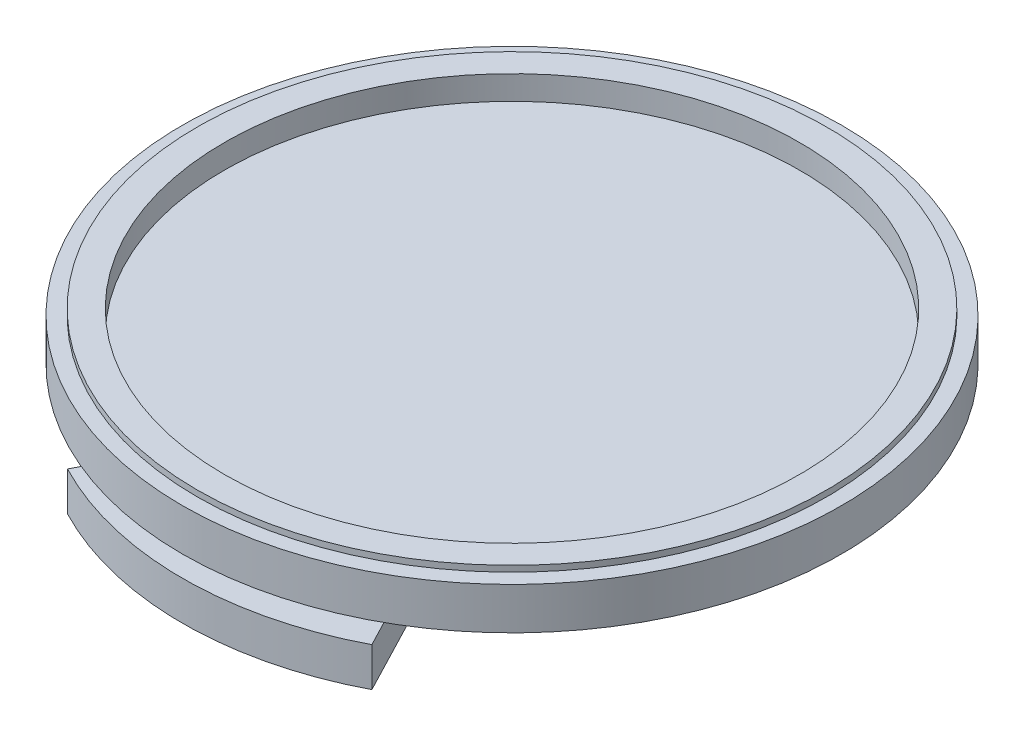
SolidWorks part; units mm, degrees
material "Nickel"
ref_plane "Front Plane" through (0, 0, 0) normal (0, 0, 1) x (1, 0, 0)
ref_plane "Top Plane" through (0, 0, 0) normal (0, 1, 0) x (1, 0, 0)
ref_plane "Right Plane" through (0, 0, 0) normal (1, 0, 0) x (0, 0, -1)
sketch "Sketch1" plane through (0, 0, 0) normal (1, 0, 0) x (0, 0, -1)
  line L0 (0, 0) -> (6.6548, 0)
  line L1 (6.6548, 0) -> (6.6548, 1.651)
  line L2 (6.6548, 1.651) -> (12.5222, 1.651)
  line L3 (12.5222, 1.651) -> (12.5222, 2.54)
  line L4 (12.5222, 2.54) -> (13.97, 2.54)
  line L5 (13.97, 2.54) -> (13.97, 4.318)
  line L6 (13.97, 4.318) -> (13.335, 4.318)
  line L7 (13.335, 4.318) -> (13.335, 4.572)
  line L8 (13.335, 4.572) -> (12.192, 4.572)
  line L9 (0, 3.556) -> (0, 0)
  line L10 (12.192, 4.572) -> (12.192, 3.556)
  line L11 (12.192, 3.556) -> (0, 3.556)
  dimension "D1" = 13.97
  dimension "D2" = 4.572
  dimension "D3" = 0.254
  dimension "D4" = 13.335
  dimension "D5" = 6.6548
  dimension "D6" = 12.5222
  dimension "D7" = 1.651
  dimension "D8" = 0.889
  dimension "D9" = 1.016
  dimension "D10" = 12.192
revolve "Revolve1" add sketch "Sketch1" angle 360 about L9
sketch "Sketch2" plane through (0, 1.651, 0) normal (0, -1, 0) x (1, 0, 0)
  line L0 (-6.4506, 12.3915) -> (0, 0) construction
  line L1 (0, 0) -> (6.4506, 12.3915) construction
  line L2 (-3.8704, 7.4349) -> (-6.4506, 12.3915)
  line L3 (3.8704, 7.4349) -> (6.4506, 12.3915)
  arc A0 (-6.4506, 12.3915) -> (6.4506, 12.3915) centre (0, 0) cw
  circle A1 centre (0, 0) radius 13.97 construction
  arc A2 (-3.8704, 7.4349) -> (3.8704, 7.4349) centre (0, 0) cw
  point P7 (0, 8.382)
  dimension "D3" = 8.382
  dimension "D1" = 12.9013
  dimension "D2" = 55
extrude "Boss-Extrude1" add sketch "Sketch2" along normal up to surface (1.651 mm away) up to face at (0, 0, 6.6548)
